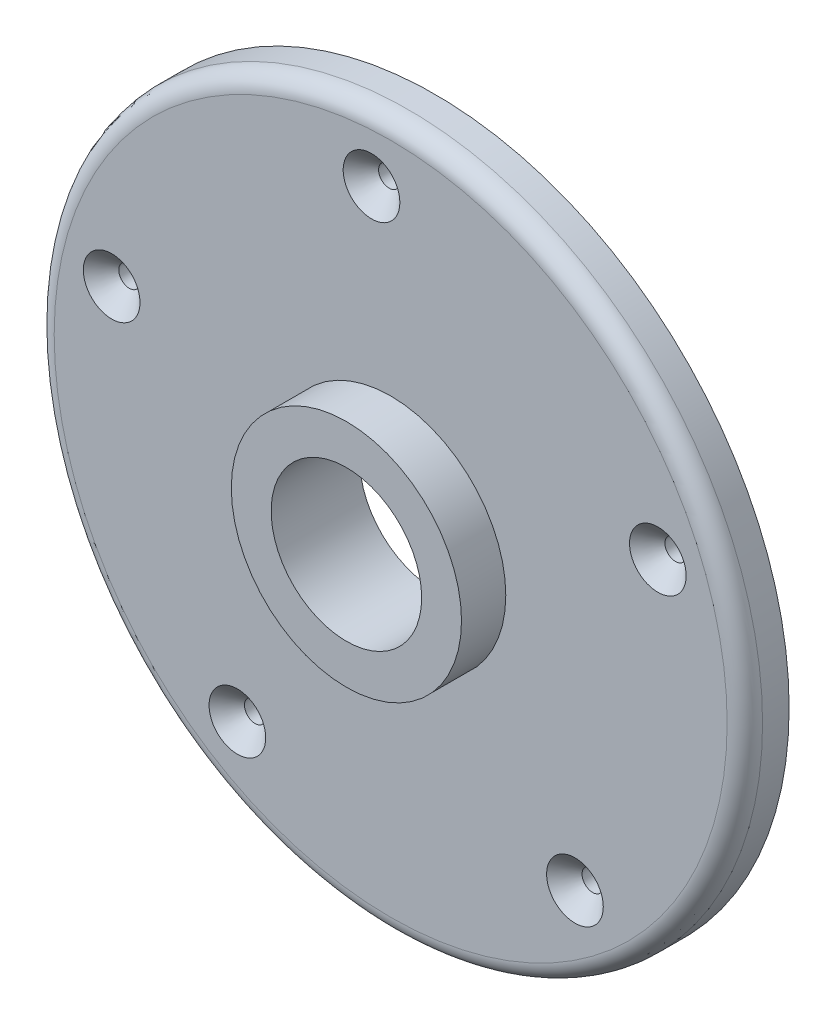
SolidWorks part; units mm, degrees
material "AISI 1020"
ref_plane "Front Plane" through (0, 0, 0) normal (0, 0, 1) x (1, 0, 0)
ref_plane "Top Plane" through (0, 0, 0) normal (0, 1, 0) x (1, 0, 0)
ref_plane "Right Plane" through (0, 0, 0) normal (1, 0, 0) x (0, 0, -1)
sketch "Sketch1" plane through (0, 0, 0) normal (0, 0, 1) x (1, 0, 0)
  circle A0 centre (0, 0) radius 40
  circle A1 centre (0, 0) radius 8.5
  dimension "D1" = 17
  dimension "D2" = 80
extrude "Boss-Extrude1" add sketch "Sketch1" along normal mid plane 5
fillet "Fillet2" radius 2 1 edges at (40, 0, 2.5)
sketch "Sketch4" plane through (0, 0, 2.5) normal (0, 0, 1) x (1, 0, 0)
  circle A0 centre (0, 0) radius 32.5
  circle A1 centre (-2.1628, 32.428) radius 2.5
  circle A2 centre (30.1725, 12.0777) radius 2.5
  circle A3 centre (20.8104, -24.9635) radius 2.5
  circle A4 centre (-17.3109, -27.506) radius 2.5
  circle A5 centre (-31.5092, 7.9639) radius 2.5
  point P16 (0, 0)
  dimension "D1" = 5
  dimension "D2" = 65
hole_wizard "CSK for M2 Flat Head Machine Screw1" positions "3DSketch2" profile "Sketch5" countersink size "M2" standard "ANSI Metric" end condition through all
sketch3d "3DSketch2"
  point P0 (-2.1628, 32.428, 2.5)
sketch "Sketch5" plane through (-2.1628, 32.428, 2.5) normal (1, 0, 0) x (0, -1, 0)
  line L0 (0, 0) -> (0, 5)
  line L1 (0, 5) -> (1.225, 5)
  line L2 (1.2, 4.975) -> (1.2, 2)
  line L3 (1.2, 2) -> (3.2, 0)
  line L5 (3.2, 0) -> (0, 0)
  line L6 (-1.2, 2) -> (-3.2, 0) construction
  line L7 (1.225, 5) -> (1.2, 4.975)
  line L8 (-1.225, 5) -> (-1.2, 4.975) construction
  line L11 (0, -6.35) -> (0, 107.95) construction
  dimension "Thru Hole Dia." = 2.4
  dimension "Thru Hole Depth" = 5
  dimension "Near C'Sink Dia." = 6.4
  dimension "Near C'Sink Angle" = 90
  dimension "Far C'Sink Dia." = 2.45
  dimension "Far C'Sink Angle" = 90
pattern_circular "CirPattern1" count 5 over 360 about axis through (0, 0, 0) along (0, 0, 1) of "CSK for M2 Flat Head Machine Screw1"
sketch "Sketch6" plane through (0, 0, 2.5) normal (0, 0, 1) x (1, 0, 0)
  circle A0 centre (0, 0) radius 13
  circle A1 centre (0, 0) radius 8.5
  dimension "D1" = 26
  dimension "D2" = 17
extrude "Boss-Extrude2" add sketch "Sketch6" along normal blind 5
